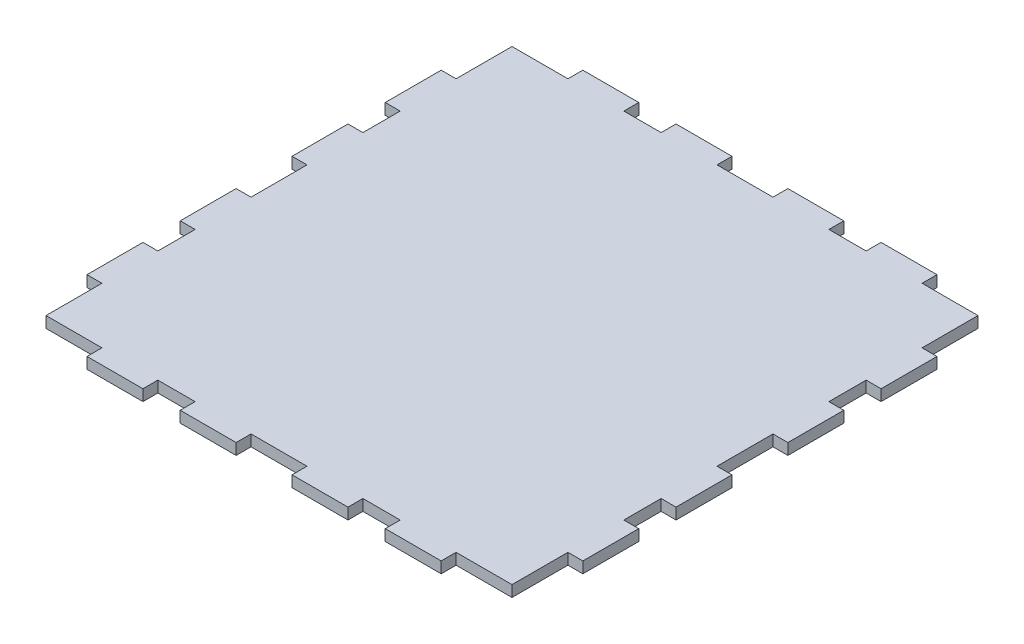
SolidWorks part; units mm, degrees
material "Oak"
ref_plane "Front Plane" through (0, 0, 0) normal (0, 0, 1) x (1, 0, 0)
ref_plane "Top Plane" through (0, 0, 0) normal (0, 1, 0) x (1, 0, 0)
ref_plane "Right Plane" through (0, 0, 0) normal (1, 0, 0) x (0, 0, -1)
sketch "Sketch1" plane through (0, 0, 0) normal (0, 1, 0) x (1, 0, 0)
  line L0 (-1.5, 0) -> (-62.5, 0) construction
  line L6 (7.5, -66.5) -> (7.5, -62.5)
  line L11 (-7.5, -62.5) -> (7.5, -62.5)
  line L12 (-7.5, -66.5) -> (-7.5, -62.5)
  line L14 (7.5, -66.5) -> (22.5, -66.5)
  line L15 (62.5, -59) -> (62.5, -62.5)
  line L31 (57.5, -62.5) -> (47.5, -62.5)
  line L32 (47.5, -62.5) -> (47.5, -66.5)
  line L33 (32.5, -62.5) -> (22.5, -62.5)
  line L34 (22.5, -62.5) -> (22.5, -66.5)
  line L35 (-22.5, -62.5) -> (-22.5, -66.5)
  line L36 (-32.5, -62.5) -> (-22.5, -62.5)
  line L37 (-32.5, -62.5) -> (-32.5, -66.5)
  line L39 (-47.5, -62.5) -> (-47.5, -66.5)
  line L40 (-59, -62.5) -> (-47.5, -62.5)
  line L41 (-22.5, -66.5) -> (-7.5, -66.5)
  line L42 (-47.5, -66.5) -> (-32.5, -66.5)
  line L44 (32.5, -62.5) -> (32.5, -66.5)
  line L45 (32.5, -66.5) -> (47.5, -66.5)
  line L61 (62.5, -47.5) -> (62.5, -59)
  line L62 (66.5, -47.5) -> (62.5, -47.5)
  line L63 (62.5, -22.5) -> (62.5, -32.5)
  line L64 (62.5, -32.5) -> (66.5, -32.5)
  line L65 (66.5, -22.5) -> (62.5, -22.5)
  line L69 (-62.5, -47.5) -> (-62.5, -59)
  line L70 (-66.5, -47.5) -> (-62.5, -47.5)
  line L71 (-62.5, -32.5) -> (-66.5, -32.5)
  line L72 (-62.5, -22.5) -> (-62.5, -32.5)
  line L73 (-66.5, -22.5) -> (-62.5, -22.5)
  line L85 (66.5, -32.5) -> (66.5, -47.5)
  line L87 (62.5, -62.5) -> (57.5, -62.5)
  line L92 (-62.5, -59) -> (-62.5, -62.5)
  line L93 (-62.5, -62.5) -> (-59, -62.5)
  line L96 (-66.5, -32.5) -> (-66.5, -47.5)
  line L101 (66.5, -22.5) -> (66.5, -7.5)
  line L102 (-66.5, -22.5) -> (-66.5, -7.5)
  line L103 (66.5, -7.5) -> (62.5, -7.5)
  line L104 (62.5, -7.5) -> (62.5, 7.5)
  line L105 (-66.5, -7.5) -> (-62.5, -7.5)
  line L106 (-62.5, -7.5) -> (-62.5, 7.5)
  line L107 (-66.5, 7.5) -> (-62.5, 7.5)
  line L108 (66.5, 7.5) -> (62.5, 7.5)
  line L109 (-66.5, 22.5) -> (-66.5, 7.5)
  line L110 (66.5, 22.5) -> (66.5, 7.5)
  line L111 (-66.5, 32.5) -> (-66.5, 47.5)
  line L112 (-62.5, 62.5) -> (-59, 62.5)
  line L113 (-62.5, 59) -> (-62.5, 62.5)
  line L114 (62.5, 62.5) -> (57.5, 62.5)
  line L115 (66.5, 32.5) -> (66.5, 47.5)
  line L116 (-66.5, 22.5) -> (-62.5, 22.5)
  line L117 (-62.5, 22.5) -> (-62.5, 32.5)
  line L118 (-62.5, 32.5) -> (-66.5, 32.5)
  line L119 (-66.5, 47.5) -> (-62.5, 47.5)
  line L120 (-62.5, 47.5) -> (-62.5, 59)
  line L121 (66.5, 22.5) -> (62.5, 22.5)
  line L122 (62.5, 32.5) -> (66.5, 32.5)
  line L123 (62.5, 22.5) -> (62.5, 32.5)
  line L124 (66.5, 47.5) -> (62.5, 47.5)
  line L125 (62.5, 47.5) -> (62.5, 59)
  line L126 (32.5, 66.5) -> (47.5, 66.5)
  line L127 (32.5, 62.5) -> (32.5, 66.5)
  line L128 (-47.5, 66.5) -> (-32.5, 66.5)
  line L129 (-22.5, 66.5) -> (-7.5, 66.5)
  line L130 (-59, 62.5) -> (-47.5, 62.5)
  line L131 (-47.5, 62.5) -> (-47.5, 66.5)
  line L132 (-32.5, 62.5) -> (-32.5, 66.5)
  line L133 (-32.5, 62.5) -> (-22.5, 62.5)
  line L134 (-22.5, 62.5) -> (-22.5, 66.5)
  line L135 (22.5, 62.5) -> (22.5, 66.5)
  line L136 (32.5, 62.5) -> (22.5, 62.5)
  line L137 (47.5, 62.5) -> (47.5, 66.5)
  line L138 (57.5, 62.5) -> (47.5, 62.5)
  line L139 (62.5, 59) -> (62.5, 62.5)
  line L140 (7.5, 66.5) -> (22.5, 66.5)
  line L141 (-7.5, 66.5) -> (-7.5, 62.5)
  line L142 (-7.5, 62.5) -> (7.5, 62.5)
  line L143 (7.5, 66.5) -> (7.5, 62.5)
  point P11 (-47.5, -64.5)
  point P12 (-62.5, 0)
  point P18 (62.5, 0)
  dimension "D4" = 10
  dimension "D5" = 15
  dimension "D6" = 15
  dimension "D7" = 15
  dimension "D8" = 15
  dimension "D9" = 15
  dimension "D10" = 15
  dimension "D11" = 15
  dimension "D12" = 62.5
  dimension "D13" = 10
  dimension "D14" = 7.5
  dimension "D15" = 62.5
  dimension "D16" = 62.5
  dimension "D17" = 15
  dimension "D26" = 15
  dimension "D27" = 15
  dimension "D28" = 15
  dimension "D30" = 10
extrude "Boss-Extrude1" add sketch "Sketch1" along normal blind 3
sketch "Sketch2" plane through (0, 0, 0) normal (0, -1, 0) x (1, 0, 0)
  circle A0 centre (0, 0) radius 25
  circle A1 centre (0, 0) radius 17.5
extrude "Boss-Extrude2" add sketch "Sketch2" along normal blind 10
